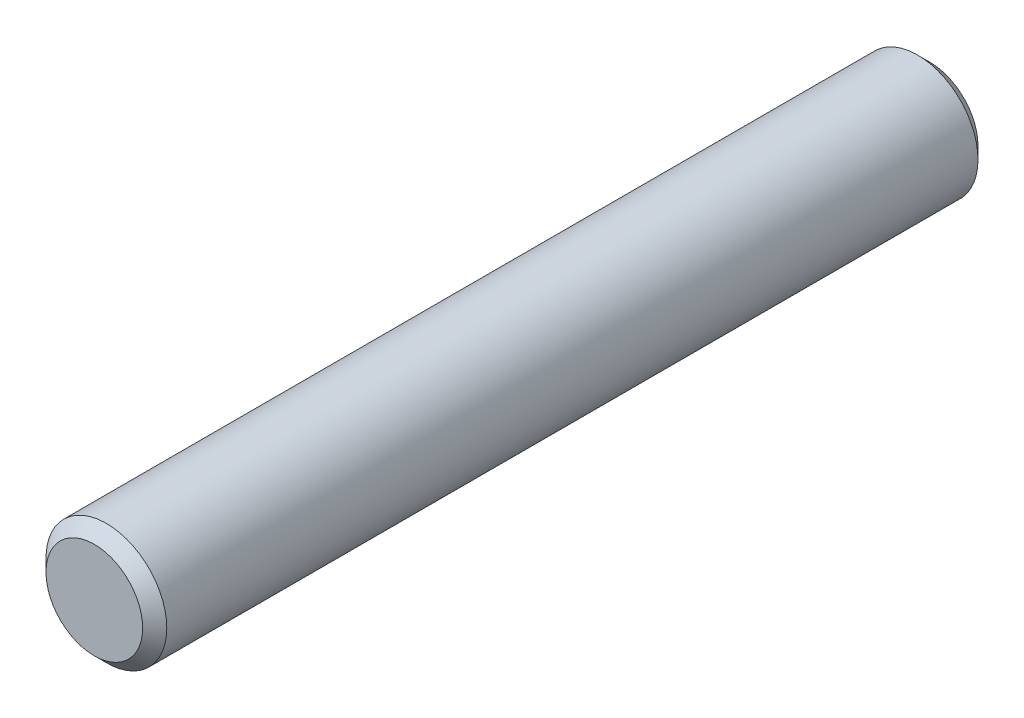
SolidWorks part; units mm, degrees
ref_plane "Front" through (0, 0, 0) normal (0, 0, 1) x (1, 0, 0)
ref_plane "Top" through (0, 0, 0) normal (0, 1, 0) x (1, 0, 0)
ref_plane "Right" through (0, 0, 0) normal (1, 0, 0) x (0, 0, -1)
sketch "Sketch1" plane through (0, 0, 0) normal (0, 0, 1) x (1, 0, 0)
  circle A0 centre (0, 0) radius 3
  dimension "dia" = 6
extrude "Extrude1" add sketch "Sketch1" along normal mid plane 41.5
sketch "Sketch2" plane through (0, 0, 0) normal (1, 0, 0) x (0, 0, -1)
  point P0 (-20.75, 3)
  point P1 (20.75, 3)
chamfer "Chamfer1" distance 0.6 angle 45 2 edges at (3, 0, -20.75) (3, 0, 20.75)
equation "\"D1@Chamfer1\" = \"dia@Sketch1\" * .1"
